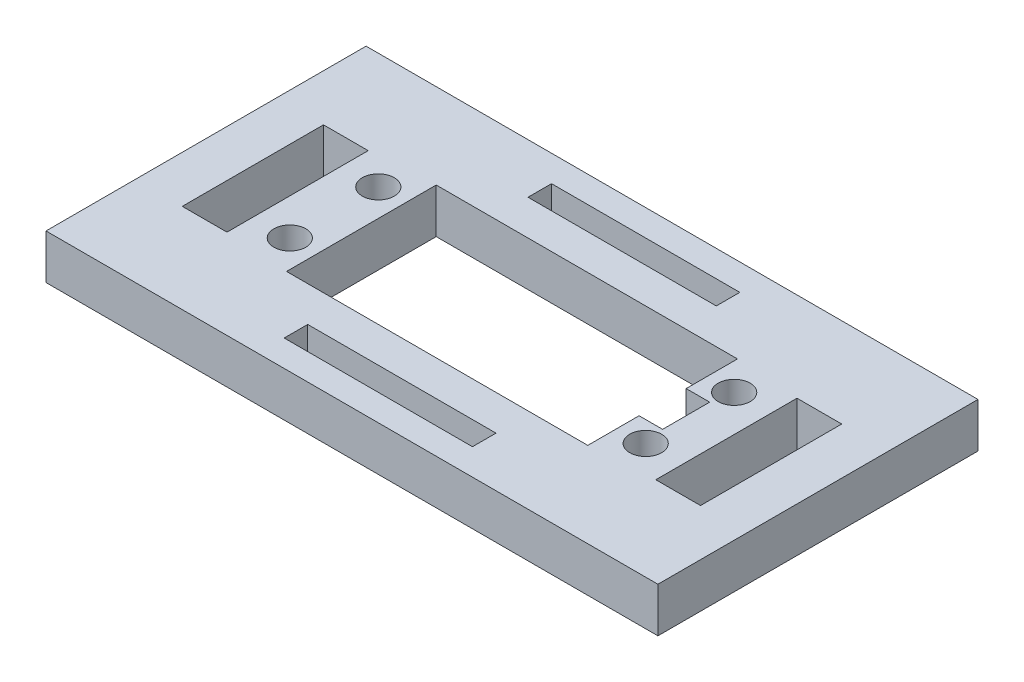
SolidWorks part; units mm, degrees
ref_plane "Front" through (0, 0, 0) normal (0, 0, 1) x (1, 0, 0)
ref_plane "Top" through (0, 0, 0) normal (0, 1, 0) x (1, 0, 0)
ref_plane "Right" through (0, 0, 0) normal (1, 0, 0) x (0, 0, -1)
sketch "Sketch1" plane through (0, 0, 0) normal (0, 1, 0) x (1, 0, 0)
  line L0 (0, 10.0965) -> (40.64, 10.0965) construction
  line L1 (0, 0) -> (40.64, 0)
  line L2 (0, 0) -> (0, 20.193)
  line L3 (0, 20.193) -> (40.64, 20.193)
  line L4 (40.64, 0) -> (40.64, 20.193)
  line L5 (-20.955, -11.4935) -> (61.595, -11.4935)
  line L6 (-20.955, -11.4935) -> (-20.955, 31.6865)
  line L7 (-20.955, 31.6865) -> (61.595, 31.6865)
  line L8 (61.595, -11.4935) -> (61.595, 31.6865)
  line L9 (44.323, 16.0655) -> (44.323, 4.1275) construction
  line L10 (20.32, 20.193) -> (20.32, 0) construction
  line L11 (7.62, -7.9375) -> (33.02, -7.9375)
  line L12 (7.62, 24.9555) -> (33.02, 24.9555)
  line L13 (7.62, 24.9555) -> (7.62, 28.1305)
  line L14 (7.62, 28.1305) -> (33.02, 28.1305)
  line L15 (33.02, 24.9555) -> (33.02, 28.1305)
  line L16 (-14.6368, 19.6215) -> (-8.6043, 19.6215)
  line L17 (-14.6368, 19.6215) -> (-14.6367, 0.5715)
  line L18 (-14.6367, 0.5715) -> (-8.6042, 0.5715)
  line L19 (-8.6043, 19.6215) -> (-8.6042, 0.5715)
  line L20 (33.02, -4.7625) -> (33.02, -7.9375)
  line L21 (7.62, -4.7625) -> (33.02, -4.7625)
  line L22 (7.62, -4.7625) -> (7.62, -7.9375)
  line L23 (55.2767, 0.5715) -> (49.2443, 0.5715)
  line L24 (49.2443, 19.6215) -> (49.2443, 0.5715)
  line L25 (55.2767, 19.6215) -> (49.2443, 19.6215)
  line L26 (55.2767, 19.6215) -> (55.2767, 0.5715)
  circle A0 centre (44.323, 16.0655) radius 2.159
  circle A1 centre (44.323, 4.1275) radius 2.159
  circle A2 centre (-3.683, 4.1275) radius 2.159
  circle A3 centre (-3.683, 16.0655) radius 2.159
  point P12 (20.32, 31.6865)
  point P14 (-20.955, 10.0965)
  point P19 (44.323, 10.0965)
  point P20 (20.32, 28.1305)
  point P22 (7.62, 26.543)
  point P35 (-8.6042, 10.0965)
  point P36 (-11.6205, 0.5715)
  dimension "D5" = 4.318
  dimension "D1" = 20.193
  dimension "D2" = 40.64
  dimension "D3" = 82.55
  dimension "D4" = 43.18
  dimension "D6" = 4.1275
  dimension "D7" = 3.683
  dimension "D8" = 3.175
  dimension "D9" = 25.4
  dimension "D10" = 6.35
  dimension "D11" = 6.0325
  dimension "D12" = 19.05
  dimension "D13" = 7.9375
extrude "Boss-Extrude1" add sketch "Sketch1" along normal blind 6.0325
sketch "Sketch2" plane through (0, 6.0325, 0) normal (0, 1, 0) x (1, 0, 0)
  line L0 (40.64, 0) -> (40.64, 20.193) construction
  line L1 (40.64, 13.2715) -> (43.815, 13.2715)
  line L2 (40.64, 13.2715) -> (40.64, 6.9215)
  line L3 (40.64, 6.9215) -> (43.815, 6.9215)
  line L4 (43.815, 13.2715) -> (43.815, 6.9215)
  point P6 (40.64, 10.0965)
  point P7 (43.815, 10.0965)
  dimension "D1" = 6.35
  dimension "D2" = 3.175
extrude "Cut-Extrude1" cut sketch "Sketch2" against normal up to surface (6.0325 mm away) up to face at (-3.683, 0, -6.2865)
sketch "Sketch3" [suppressed] plane through (0, 6.0325, 0) normal (0, 1, 0) x (1, 0, 0)
  line L0 (-8.6042, 0.5715) -> (-8.6042, 19.6215) construction
  line L1 (-8.6042, 20.193) -> (49.2443, 20.193)
  line L2 (-8.6042, 20.193) -> (-8.6042, 0)
  line L3 (-8.6042, 0) -> (49.2443, 0)
  line L4 (49.2443, 20.193) -> (49.2443, 0)
  line L5 (49.2443, 19.6215) -> (49.2443, 0.5715) construction
  line L6 (0, 0) -> (40.64, 0) construction
  line L7 (40.64, 20.193) -> (0, 20.193) construction
extrude "Boss-Extrude2" [suppressed] add sketch "Sketch3" against normal up to surface (6.0325 mm away)
sketch "Sketch4" [suppressed] plane through (0, 6.0325, 0) normal (0, 1, 0) x (1, 0, 0)
  line L0 (61.595, -11.4935) -> (61.595, 31.6865) construction
  line L1 (-20.955, -11.4935) -> (61.595, -11.4935) construction
  line L2 (61.595, 10.0965) -> (-20.955, 10.0965) construction
  line L3 (-20.955, 31.6865) -> (-20.955, -11.4935) construction
  line L5 (61.595, 31.6865) -> (-20.955, 31.6865) construction
  line L6 (20.32, 31.6865) -> (20.32, -11.4935) construction
  circle A0 centre (48.895, -5.1435) radius 2.0193
  circle A1 centre (-8.255, -5.1435) radius 2.0193
  circle A2 centre (-8.255, 25.3365) radius 2.0193
  circle A3 centre (48.895, 25.3365) radius 2.0193
  dimension "D3" = 4.0386
  dimension "D1" = 12.7
  dimension "D2" = 6.35
extrude "Cut-Extrude2" [suppressed] cut sketch "Sketch4" against normal up to surface (6.0325 mm away)
